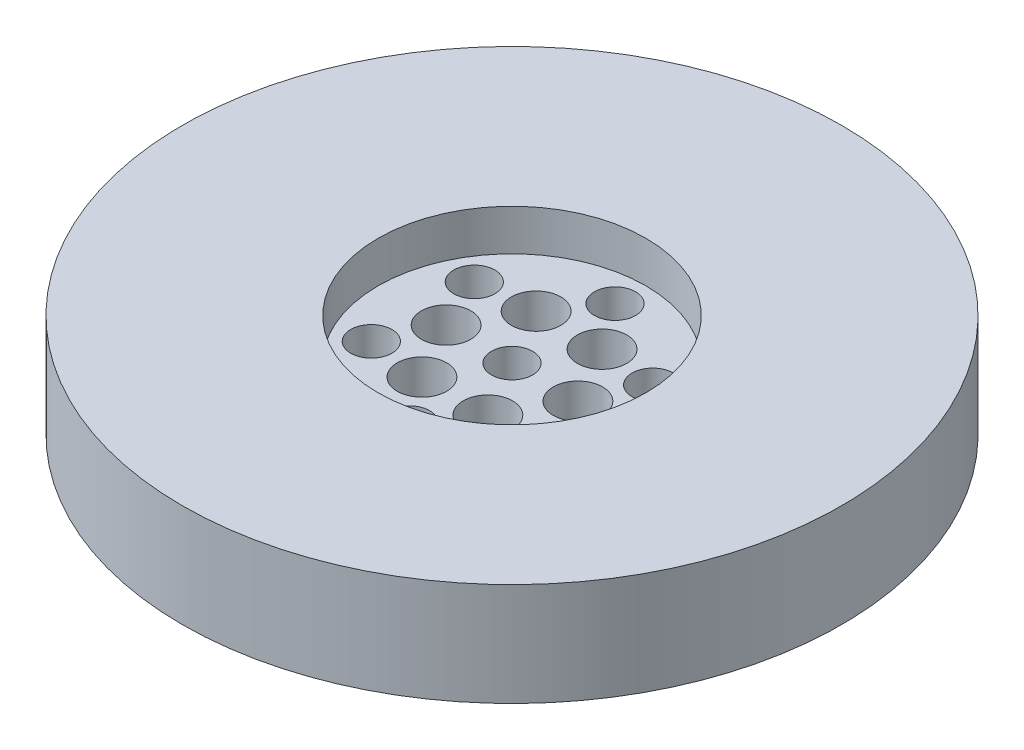
SolidWorks part; units mm, degrees
ref_plane "Front Plane" through (0, 0, 0) normal (0, 0, 1) x (1, 0, 0)
ref_plane "Top Plane" through (0, 0, 0) normal (0, 1, 0) x (1, 0, 0)
ref_plane "Right Plane" through (0, 0, 0) normal (1, 0, 0) x (0, 0, -1)
sketch "Sketch1" plane through (0, 0, 0) normal (0, 1, 0) x (1, 0, 0)
  circle A0 centre (0, 0) radius 16
  point P3 (0, 0)
  point P4 (0, 0)
  point P5 (0, 0)
extrude "Boss-Extrude1" add sketch "Sketch1" along normal blind 5
sketch "Sketch2" plane through (0, 5, 0) normal (0, 1, 0) x (1, 0, 0)
  circle A0 centre (0, 0) radius 6.5
  point P3 (0, 0)
  point P4 (0, 0)
extrude "Cut-Extrude2" cut sketch "Sketch2" against normal blind 2 contours A0
sketch "Sketch3" plane through (0, 3, 0) normal (0, 1, 0) x (1, 0, 0)
  circle A0 centre (0, 0) radius 1
  point P3 (0, 0)
  point P4 (0, 0)
extrude "Cut-Extrude3" cut sketch "Sketch3" against normal blind 3
sketch "Sketch4" plane through (0, 3, 0) normal (0, 1, 0) x (1, 0, 0)
  circle A0 centre (3.2, 0) radius 1.2
  point P2 (0, 0)
extrude "Cut-Extrude4" cut sketch "Sketch4" against normal blind 3 contours A0
sketch "Sketch6" plane through (0, 3, 0) normal (0, 1, 0) x (1, 0, 0)
  circle A0 centre (0, 5) radius 1
extrude "Cut-Extrude6" cut sketch "Sketch6" against normal blind 3
pattern_circular "CirPattern3" count 6 over 360 about axis through (0, 0, 0) along (0, 1, 0) of "Cut-Extrude6"
pattern_circular "CirPattern5" count 6 over 360 about axis through (0, 0, 0) along (0, 1, 0) of "Cut-Extrude4"
